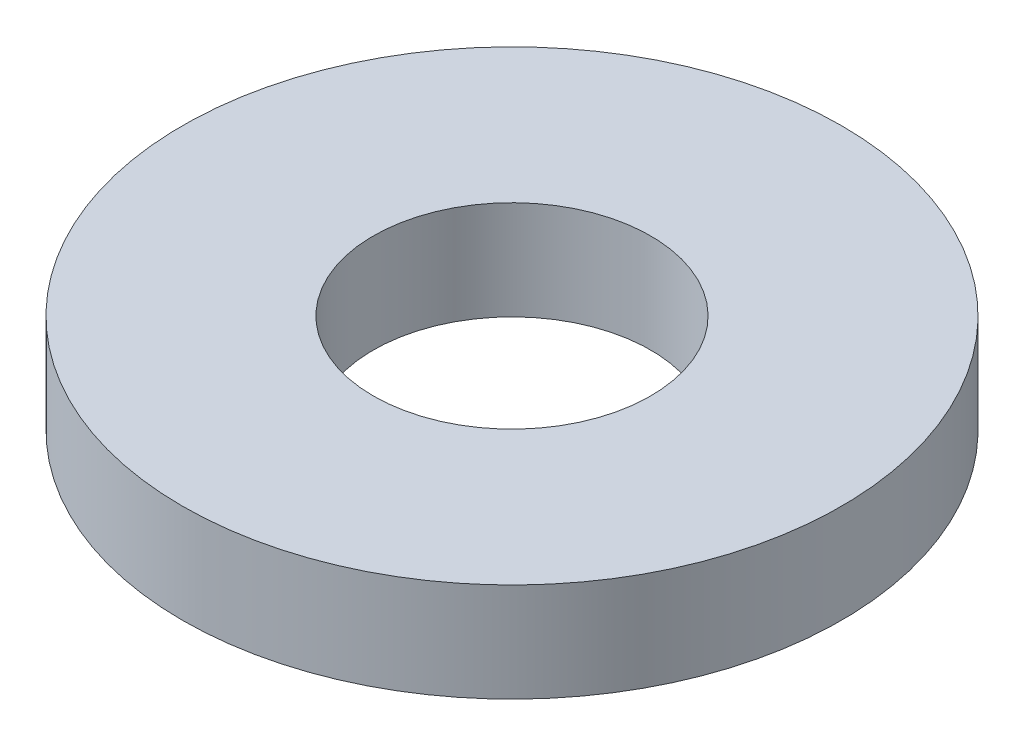
SolidWorks part; units mm, degrees
ref_plane "Front Plane" through (0, 0, 0) normal (0, 0, 1) x (1, 0, 0)
ref_plane "Top Plane" through (0, 0, 0) normal (0, 1, 0) x (1, 0, 0)
ref_plane "Right Plane" through (0, 0, 0) normal (1, 0, 0) x (0, 0, -1)
sketch "Sketch1" plane through (0, 0, 0) normal (0, 1, 0) x (1, 0, 0)
  circle A0 centre (0, 0) radius 15.875
  circle A1 centre (0, 0) radius 6.6802
  dimension "D1" = 13.3604
  dimension "D2" = 31.75
extrude "Extrude1" add sketch "Sketch1" against normal blind 4.7625
